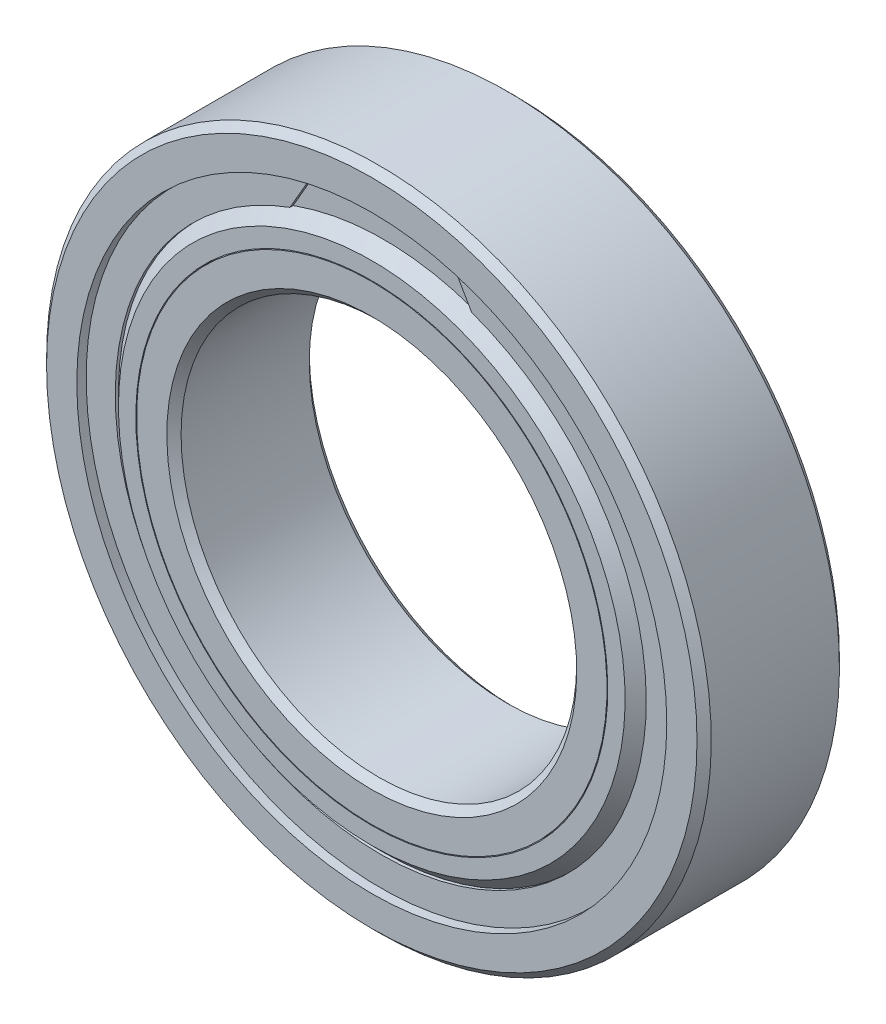
SolidWorks part; units mm, degrees
ref_plane "Front Plane" through (0, 0, 0) normal (0, 0, 1) x (1, 0, 0)
ref_plane "Top Plane" through (0, 0, 0) normal (0, 1, 0) x (1, 0, 0)
ref_plane "Right Plane" through (0, 0, 0) normal (1, 0, 0) x (0, 0, -1)
sketch "Sketch1" plane through (0, 0, 0) normal (0, 0, 1) x (1, 0, 0)
  circle A0 centre (0, 0) radius 21
  circle A1 centre (0, 0) radius 12.5
  dimension "OD" = 42
  dimension "ID" = 25
  dimension "For Shaft Diameter" = 25
sketch "Sketch8" plane through (0, 0, 0) normal (1, 0, 0) x (0, 0, -1)
  line L1 (-4.5, 21) -> (4.5, 21)
  line L2 (-4.5, 21) -> (-4.5, -21)
  line L3 (-4.5, -21) -> (4.5, -21)
  line L4 (4.5, 21) -> (4.5, -21)
  line L5 (-4.5, 21) -> (4.5, -21) construction
  line L6 (-4.5, -21) -> (4.5, 21) construction
  point P0 (0, 0)
  point P6 (0, -21)
  dimension "Width" = 9
sketch "Sketch5" plane through (0, 0, 0) normal (1, 0, 0) x (0, 0, -1)
  line L0 (-4.5, 0) -> (4.5, 0) construction
  line L1 (0, 21) -> (0, -21) construction
  line L2 (4.05, 21) -> (-4.05, 21)
  line L3 (-4.05, 21) -> (-4.5, 20.55)
  line L4 (-4.5, 20.55) -> (-4.5, 18.6389)
  line L5 (-4.5, 18.6389) -> (-2, 18.6389)
  line L6 (4.5, 18.6389) -> (2, 18.6389)
  line L7 (4.5, 20.55) -> (4.5, 18.6389)
  line L8 (4.05, 21) -> (4.5, 20.55)
  line L9 (0, 21) -> (0, 16.75) construction
  line L10 (0, 16.75) -> (0, 12.5) construction
  line L11 (-2.5838, 17.6944) -> (-4.5, 17.6944) construction
  line L12 (3.3514, 16.7754) -> (3.7324, 16.7754)
  line L13 (-3.3514, 16.7754) -> (-3.7324, 16.7754)
  line L14 (-3.3514, 16.7754) -> (-3.3514, 18.6135)
  line L15 (-3.3514, 18.6135) -> (-3.7324, 18.6135)
  line L16 (-3.7324, 16.7754) -> (-3.7324, 18.6135)
  line L17 (-3.3514, 16.7754) -> (-3.7324, 18.6135) construction
  line L18 (-3.3514, 18.6135) -> (-3.7324, 16.7754) construction
  line L19 (3.7324, 16.7754) -> (3.7324, 18.6135)
  line L20 (3.3514, 18.6135) -> (3.7324, 18.6135)
  line L21 (3.3514, 16.7754) -> (3.3514, 18.6135)
  line L22 (0, 21) -> (0, -21) construction
  line L23 (4.5, 0) -> (4.5, 21) construction
  line L24 (4.5, 21) -> (4.05, 21) construction
  line L25 (-4.5, 0) -> (-4.5, 21) construction
  line L26 (-4.5, 21) -> (-4.05, 21) construction
  line L27 (4.5, 0) -> (4.5, -21) construction
  line L28 (-4.5, 0) -> (-4.5, -21) construction
  line L29 (-4.5, -21) -> (4.5, -21) construction
  line L30 (-2.751, 16.75) -> (-2.751, 18.6389) construction
  line L31 (-2.751, 17.6944) -> (-2.751, 16.75) construction
  line L32 (-2.751, 17.2222) -> (-2.751, 17.6944) construction
  arc A0 (-2, 18.6389) -> (2, 18.6389) centre (0, 16.75) cw
  circle A1 centre (0, 16.75) radius 2.751 construction
  point P14 (0, 12.5)
  point P15 (-3.5419, 17.6944)
  point P36 (-2.751, 17.6944)
  dimension "D1" = 45
  dimension "D2" = 0.45
  dimension "D3" = 4
  dimension "D4" = 1.8889
  dimension "D5" = 0.381
  dimension "D6" = 0.0254
revolve "Revolve1" add sketch "Sketch5" angle 360 about L0
sketch "Sketch3" plane through (0, 0, 0) normal (1, 0, 0) x (0, 0, -1)
  line L0 (-4.5, 14.8611) -> (-2, 14.8611)
  line L1 (0, 21) -> (0, -21) construction
  line L2 (-4.5, 20.55) -> (-4.5, 18.6389) construction
  line L3 (-4.5, 14.8611) -> (-4.5, 12.95)
  line L4 (-4.05, 21) -> (-4.5, 20.55) construction
  line L5 (-4.5, 12.95) -> (-4.05, 12.5)
  line L6 (-4.05, 12.5) -> (4.05, 12.5)
  line L7 (4.05, 21) -> (4.05, -21) construction
  line L8 (4.05, 12.5) -> (4.5, 12.95)
  line L9 (4.5, -20.55) -> (4.5, 20.55) construction
  line L10 (4.5, 12.95) -> (4.5, 14.8611)
  line L11 (4.5, 14.8611) -> (2, 14.8611)
  line L13 (4.05, 21) -> (4.5, 20.55) construction
  arc A0 (2, 18.6389) -> (-2, 18.6389) centre (0, 16.75) ccw construction
  arc A1 (2, 14.8611) -> (-2, 14.8611) centre (0, 16.75) cw
revolve "Revolve3" add sketch "Sketch3" angle 360 about L0
sketch "Sketch9" plane through (0, 0, 0) normal (1, 0, 0) x (0, 0, -1)
  line L0 (-3.7324, 16.7754) -> (-4.5, 16.0078)
  line L1 (-4.5, 0) -> (-4.5, 21) construction
  line L2 (-4.5, 16.0078) -> (-4.5, 14.9111)
  line L3 (-4.5, 14.9111) -> (-3.3514, 14.9111)
  line L4 (-3.3514, 14.9111) -> (-3.3514, 16.7754)
  line L5 (-4.5, 14.8611) -> (-2, 14.8611) construction
  line L6 (-3.7324, 16.7754) -> (-3.3514, 16.7754)
  line L7 (0, 21) -> (0, -21) construction
  line L8 (0, 21) -> (0, -21) construction
  line L9 (3.7324, 16.7754) -> (3.3514, 16.7754)
  line L10 (3.3514, 14.9111) -> (3.3514, 16.7754)
  line L11 (4.5, 14.9111) -> (3.3514, 14.9111)
  line L12 (4.5, 16.0078) -> (4.5, 14.9111)
  line L13 (3.7324, 16.7754) -> (4.5, 16.0078)
  dimension "D1" = 0.05
  dimension "D2" = 45
revolve "Revolve5" add sketch "Sketch9" angle 360 about L0
sketch "Sketch10" plane through (0, 0, 3.7324) normal (0, 0, 1) x (1, 0, 0)
  line L0 (0, 0) -> (-6.3662, 17.491) construction
  line L1 (-6.3662, 17.491) -> (6.3662, 17.491) construction
  line L2 (6.3662, 17.491) -> (0, 0) construction
  line L3 (-5.7375, 15.7637) -> (-4.3963, 18.0869)
  line L4 (0, 0) -> (0, 21) construction
  line L5 (0, 0) -> (0, 21) construction
  line L6 (5.7375, 15.7637) -> (4.3963, 18.0869)
  circle A0 centre (0, 0) radius 16.7754 construction
  circle A1 centre (0, 0) radius 18.6135
  circle A2 centre (0, 0) radius 18.6135 construction
  circle A3 centre (0, 0) radius 16.7754 construction
  circle A4 centre (0, 0) radius 18.6135 construction
  arc A7 (-5.7375, 15.7637) -> (5.7375, 15.7637) centre (0, 0) ccw
  arc A8 (4.3963, 18.0869) -> (-4.3963, 18.0869) centre (0, 0) cw
  dimension "D2" = 40
  dimension "D3" = 30
  dimension "D1" = 0
extrude "Boss-Extrude1" add sketch "Sketch10" along normal blind 0.2 separate body
mirror "Mirror2" about plane through (0, 0, 0) normal (0, 0, 1) of bodies 149
sketch "Sketch4" plane through (0, 0, 0) normal (1, 0, 0) x (0, 0, -1)
  line L0 (-2.751, 16.75) -> (2.751, 16.75)
  arc A2 (-2.751, 16.75) -> (2.751, 16.75) centre (0, 16.75) cw
  arc A3 (2, 18.6389) -> (-2, 18.6389) centre (0, 16.75) ccw construction
revolve "Revolve4" add sketch "Sketch4" angle 360 about L0
pattern_circular "CirPattern1" count 15 every 24 about axis through (0, 0, 0) along (0, 0, 1) of bodies 104
equation "\"D2@Sketch5\" = \"Width@Sketch8\" * .05"
equation "\"D3@Sketch5\" = \"Width@Sketch8\" / 2.25"
equation "\"D4@Sketch5\"=((\"OD@Sketch1\"-\"ID@Sketch1\")/2)/4.5"
equation "\"D2@CirPattern1\" = 360/\"Balls@CirPattern1\""
